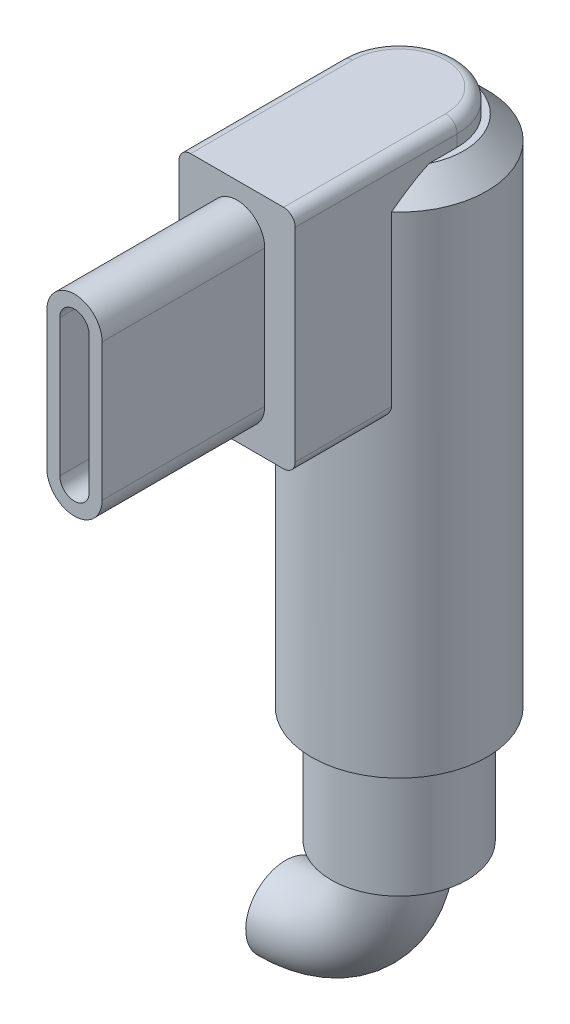
SolidWorks part; units mm, degrees
ref_plane "Front" through (0, 0, 0) normal (0, 0, 1) x (1, 0, 0)
ref_plane "Top" through (0, 0, 0) normal (0, 1, 0) x (1, 0, 0)
ref_plane "Right" through (0, 0, 0) normal (1, 0, 0) x (0, 0, -1)
sketch "Sketch1" plane through (0, 0, 0) normal (0, 1, 0) x (1, 0, 0)
  circle A0 centre (0, 0) radius 2.925
  dimension "D1" = 5.85
extrude "Boss-Extrude1" add sketch "Sketch1" along normal blind 5
sketch "Sketch2" plane through (0, 5, 0) normal (0, 1, 0) x (1, 0, 0)
  circle A0 centre (0, 0) radius 3.775
  dimension "D1" = 7.55
extrude "Boss-Extrude2" add sketch "Sketch2" along normal blind 23.1
ref_plane "Plane1" through (0, 0, 3.775) normal (0, 0, 1) x (1, 0, 0)
sketch "Sketch3" plane through (0, 0, 3.775) normal (0, 0, 1) x (1, 0, 0)
  line L0 (3.775, 28.1) -> (-3.775, 28.1) construction
  line L1 (-2.5, 28.1) -> (2.5, 28.1)
  line L2 (-2.5, 28.1) -> (-2.5, 18.35)
  line L3 (-2.5, 18.35) -> (2.5, 18.35)
  line L4 (2.5, 28.1) -> (2.5, 18.35)
  point P4 (0, 28.1)
  dimension "D1" = 5
  dimension "D2" = 9.75
extrude "Boss-Extrude3" add sketch "Sketch3" along normal blind 3.2 and the other way up to next
sketch "Sketch4" plane through (0, 0, 6.975) normal (0, 0, 1) x (1, 0, 0)
  line L0 (0, 26.175) -> (0, 20.275) construction
  line L1 (1.19, 26.175) -> (1.19, 20.275)
  line L2 (-1.19, 26.175) -> (-1.19, 20.275)
  line L3 (-2.5, 23.225) -> (0, 23.225) construction
  line L4 (-2.5, 28.1) -> (-2.5, 18.35) construction
  line L5 (0, 26.175) -> (0, 20.275) construction
  line L6 (0.63, 26.175) -> (0.63, 20.275)
  line L7 (-0.63, 26.175) -> (-0.63, 20.275)
  arc A0 (1.19, 26.175) -> (-1.19, 26.175) centre (0, 26.175) ccw
  arc A1 (-1.19, 20.275) -> (1.19, 20.275) centre (0, 20.275) ccw
  arc A2 (0.63, 26.175) -> (-0.63, 26.175) centre (0, 26.175) ccw
  arc A3 (-0.63, 20.275) -> (0.63, 20.275) centre (0, 20.275) ccw
  point P3 (0, 23.225)
  point P8 (0, 27.365)
  point P9 (0, 19.085)
  point P16 (0, 23.225)
  dimension "D1" = 8.28
  dimension "D2" = 2.38
  dimension "D3" = 0.56
extrude "Boss-Extrude4" add sketch "Sketch4" along normal blind 7
sketch "Sketch5" plane through (0, 28.1, 0) normal (0, 1, 0) x (1, 0, 0)
  line L0 (2.5, 0) -> (2.5, -2.8285)
  line L1 (-2.5, 0) -> (-2.5, -2.8285)
  line L5 (-2.5, -2.8285) -> (-2.5, -6.975)
  line L6 (-2.5, -6.975) -> (2.5, -6.975)
  line L7 (2.5, -6.975) -> (2.5, -2.8285)
  arc A0 (2.5, 0) -> (-2.5, 0) centre (0, 0) ccw
  arc A2 (2.5, -2.8285) -> (-2.5, -2.8285) centre (0, 0) ccw
  arc A3 (2.5, -2.8285) -> (-2.5, -2.8285) centre (0, 0) ccw
  dimension "D1" = 0
extrude "Cut-Extrude1" cut sketch "Sketch5" against normal blind 1
chamfer "Chamfer1" distance 1 angle 45 1 edges at (0, 27.1, -3.775)
fillet "Fillet1" radius 0.5 5 edges at (-2.5, 18.35, 4.9018) (-2.5, 28.1, 3.4875) (0, 28.1, -2.5) (2.5, 18.35, 4.9018) (2.5, 28.1, 3.4875)
sketch "Sketch6" plane through (0, 0, 0) normal (0, -1, 0) x (1, 0, 0)
  line L0 (-4.8895, -6.8935) -> (-4.8895, 10.2792) construction
  line L1 (-1.7145, 0) -> (-4.8895, 0) construction
  circle A0 centre (0, 0) radius 1.7145
  point P7 (-1.7145, 0)
  dimension "D1" = 3.429
  dimension "D2" = 3.175
revolve "Revolve1" add sketch "Sketch6" angle 90 about L0
